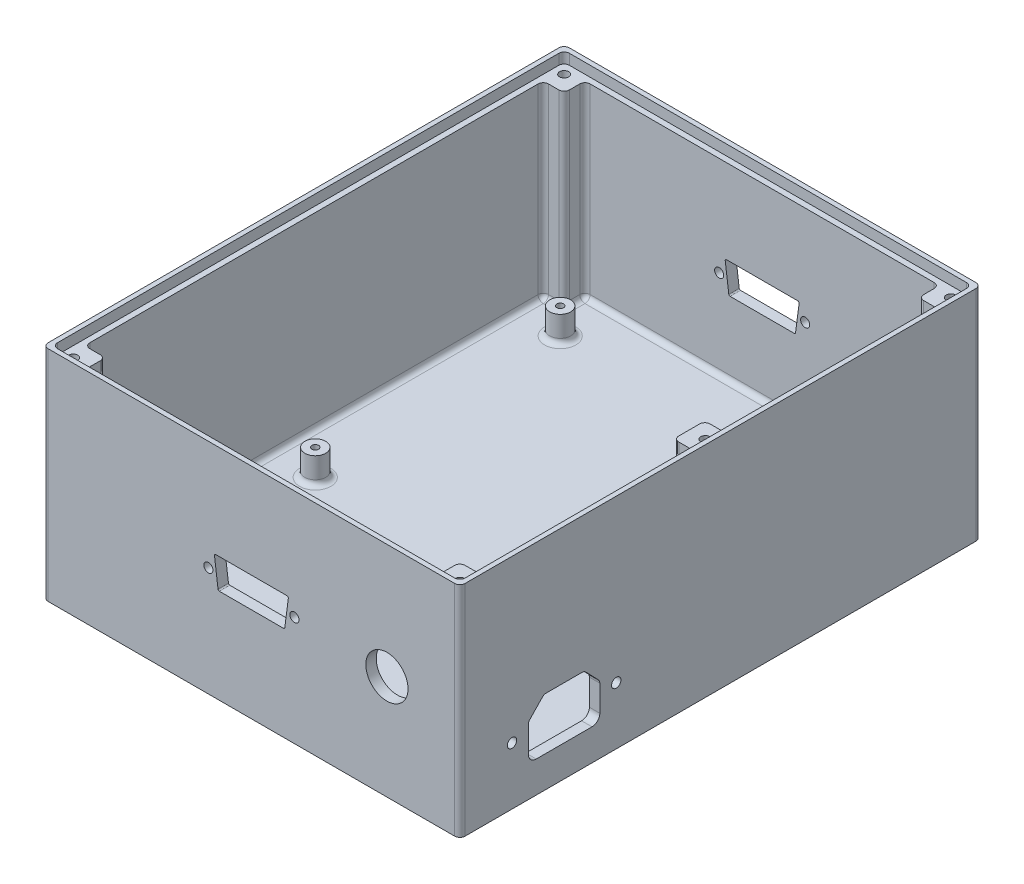
SolidWorks part; units mm, degrees
ref_plane "Front Plane" through (0, 0, 0) normal (0, 0, 1) x (1, 0, 0)
ref_plane "Top Plane" through (0, 0, 0) normal (0, 1, 0) x (1, 0, 0)
ref_plane "Right Plane" through (0, 0, 0) normal (1, 0, 0) x (0, 0, -1)
sketch "Esboço1" plane through (0, 0, 0) normal (1, 0, 0) x (0, 0, -1)
  line L0 (-100, 0) -> (100, 0)
  line L1 (100, 0) -> (100, 84)
  line L2 (100, 84) -> (-100, 84)
  line L3 (-100, 84) -> (-100, 0)
  point P4 (0, 0)
  dimension "D1" = 84
  dimension "D2" = 200
extrude "Ressalto-extrusão1" add sketch "Esboço1" along normal mid plane 160
sketch "Esboço4" plane through (0, 84, 0) normal (0, 1, 0) x (1, 0, 0)
  line L0 (0, 100) -> (0, -100) construction
  line L1 (80, 100) -> (-80, 100) construction
  line L2 (80, -100) -> (-80, -100) construction
  line L3 (-80, 0) -> (80, 0) construction
  line L4 (-80, 100) -> (-80, -100) construction
  line L5 (80, 100) -> (80, -100) construction
  line L6 (-68, -96) -> (68, -96)
  line L7 (68, -96) -> (68, -88)
  line L8 (68, -88) -> (76, -88)
  line L9 (76, -88) -> (76, -6)
  line L10 (-68, -96) -> (-68, -88)
  line L11 (-68, -88) -> (-76, -88)
  line L12 (76, -6) -> (68, -6)
  line L13 (68, -6) -> (68, 6)
  line L14 (68, 6) -> (76, 6)
  line L15 (76, 6) -> (76, 88)
  line L16 (76, 88) -> (68, 88)
  line L17 (68, 88) -> (68, 96)
  line L18 (68, 96) -> (-68, 96)
  line L19 (-68, 96) -> (-68, 88)
  line L20 (-68, 88) -> (-76, 88)
  line L21 (-76, 88) -> (-76, -88)
  circle A0 centre (-74.2, -94.2) radius 1.75
  circle A1 centre (-74.2, 94.2) radius 1.75
  circle A2 centre (74.2, -94.2) radius 1.75
  circle A3 centre (74.2, 94.2) radius 1.75
  circle A4 centre (74.2, 0) radius 1.75
  dimension "D8" = 3.5
  dimension "D2" = 4
  dimension "D3" = 12
  dimension "D4" = 6
  dimension "D5" = 12
  dimension "D6" = 6
  dimension "D7" = 4
  dimension "D9" = 5.8
  dimension "D10" = 5.8
  dimension "D11" = 5.8
  dimension "D12" = 4
extrude "Corte-extrusão1" cut sketch "Esboço4" against normal blind 76
fillet "Filete1" radius 2 10 edges at (-68, 46, 88) (-68, 46, -88) (68, 46, -88) (68, 46, 6) (68, 46, -6) (68, 46, 88) (80, 42, 100) (-80, 42, 100) (-80, 42, -100) (80, 42, -100)
sketch "Esboço7" plane through (0, 0, 0) normal (0, 0, 1) x (1, 0, 0)
  line L0 (0, 84) -> (0, 0) construction
  line L1 (78, 84) -> (-78, 84) construction
  line L2 (-80, 42) -> (80, 42) construction
  line L3 (-80, 0) -> (-80, 84) construction
  line L4 (80, 84) -> (80, 0) construction
  line L13 (-12.75, 36.25) -> (12.75, 36.25)
  line L16 (-14.25, 47.75) -> (14.25, 47.75)
  line L17 (-14.25, 47.75) -> (-12.75, 36.25)
  line L18 (14.25, 47.75) -> (12.75, 36.25)
  circle A0 centre (-16.5, 42) radius 1.75
  circle A2 centre (16.5, 42) radius 1.75
  point P21 (0, 42)
  point P22 (0, 36.25)
  point P23 (0, 47.75)
  point P24 (0, 42)
  dimension "D1" = 3.5
  dimension "D2" = 14.25
  dimension "D3" = 12.75
  dimension "D4" = 5.75
  dimension "D5" = 16.5
  dimension "D6" = 11.5
  dimension "D7" = 0
extrude "Corte-extrusão2" cut sketch "Esboço7" against normal mid plane 200
fillet "Filete3" radius 0.5 8 edges at (14.25, 47.75, -98) (-14.25, 47.75, -98) (-12.75, 36.25, -98) (12.75, 36.25, -98) (14.25, 47.75, 98) (12.75, 36.25, 98) (-12.75, 36.25, 98) (-14.25, 47.75, 98)
sketch "Esboço8" plane through (0, 0, 100) normal (0, 0, -1) x (-1, 0, 0)
  line L0 (-80, 0) -> (-80, 84) construction
  line L2 (-78, 0) -> (78, 0) construction
  circle A0 centre (-52, 40) radius 8.1
  dimension "D1" = 16.2
  dimension "D2" = 28
  dimension "D3" = 40
extrude "Corte-extrusão3" cut sketch "Esboço8" against normal up to surface (196 mm away)
sketch "Esboço9" plane through (0, 8, 0) normal (0, 1, 0) x (1, 0, 0)
  line L8 (-80, 98) -> (-80, -98) construction
  line L9 (78, 100) -> (-78, 100) construction
  line L10 (-68, -96) -> (68, -96) construction
  line L11 (0, 100) -> (0, -100) construction
  line L12 (-80, 31.5) -> (80, 31.5) construction
  line L13 (80, 98) -> (80, -98) construction
  line L14 (78, -100) -> (-78, -100) construction
  line L16 (-76, 88) -> (-76, -88) construction
  line L19 (-68, -96) -> (68, -96) construction
  circle A0 centre (-60, 78.5) radius 4
  circle A1 centre (-60, 78.5) radius 1.3
  circle A2 centre (60, 78.5) radius 1.3
  circle A3 centre (60, 78.5) radius 4
  circle A4 centre (60, -15.5) radius 4
  circle A5 centre (60, -15.5) radius 1.3
  circle A6 centre (-60, -15.5) radius 1.3
  circle A7 centre (-60, -15.5) radius 4
  circle A8 centre (-46, -86) radius 4
  circle A9 centre (-46, -86) radius 1.75
  circle A10 centre (0, -86) radius 4
  circle A11 centre (0, -86) radius 1.75
  dimension "D5" = 2.6
  dimension "D6" = 8
  dimension "D4" = 10
  dimension "D10" = 3.5
  dimension "D11" = 8
  dimension "D12" = 21.5
  dimension "D2" = 16
  dimension "D3" = 68.5
  dimension "D7" = 10
  dimension "D8" = 46
  dimension "D9" = 30
extrude "Ressalto-extrusão2" add sketch "Esboço9" along normal blind 10
sketch "Esboço11" plane through (80, 0, 0) normal (1, 0, 0) x (0, 0, -1)
  line L2 (-73.7, 15) -> (-73.7, 25.7908)
  line L3 (-70.7, 12) -> (-49.3, 12)
  line L4 (-73.7, 25.7908) -> (-67.7497, 32)
  line L5 (-67.7497, 32) -> (-52.2503, 32)
  line L6 (-60, 12) -> (-60, 32) construction
  line L7 (-46.3, 25.7908) -> (-52.2503, 32)
  line L8 (-46.3, 15) -> (-46.3, 25.7908)
  line L9 (-100, 0) -> (-100, 84) construction
  line L10 (98, 84) -> (-98, 84) construction
  line L13 (-60, 22) -> (-84.4967, 22) construction
  line L14 (-84.4967, 22) -> (-36.6459, 22) construction
  arc A1 (-73.7, 15) -> (-70.7, 12) centre (-70.7, 15) ccw
  arc A2 (-46.3, 15) -> (-49.3, 12) centre (-49.3, 15) cw
  circle A4 centre (-80, 22) radius 1.8
  circle A5 centre (-40, 22) radius 1.8
  point P21 (-60, 22)
  dimension "D1" = 133.78
  dimension "D4" = 3
  dimension "D8" = 3.6
  dimension "D2" = 8.6
  dimension "D3" = 10
  dimension "D5" = 13.7
  dimension "D6" = 40
  dimension "D7" = 52
  dimension "D9" = 20
extrude "Corte-extrusão4" cut sketch "Esboço11" against normal up to surface (4 mm away) up to face at (76, 46, 47)
fillet "Filete4" radius 2 10 edges at (76, 46, -6) (76, 46, 6) (68, 46, -96) (76, 46, -88) (-76, 46, -88) (-68, 46, -96) (-76, 46, 88) (-68, 46, 96) (68, 46, 96) (76, 46, 88)
fillet "Filete5" radius 2 38 edges at (-68.5858, 8, 88.5858) (-75.4142, 8, 87.4142) (-76, 8, 0) (-75.4142, 8, -87.4142) (-68.5858, 8, -88.5858) (-67.4142, 8, -95.4142) (0, 8, -96) (67.4142, 8, -95.4142) (68.5858, 8, -88.5858) (75.4142, 8, -87.4142) (76, 8, -47) (75.4142, 8, -6.5858) (68.5858, 8, -5.4142) (68, 8, 0) (68.5858, 8, 5.4142) (75.4142, 8, 6.5858) (76, 8, 47) (75.4142, 8, 87.4142) (68.5858, 8, 88.5858) (67.4142, 8, 95.4142) (0, 8, 96) (-60, 8, -74.5) (60, 8, -82.5) (60, 8, 19.5) (-60, 8, 11.5) (0, 8, 90) (-46, 8, 90) (-67.4142, 8, 95.4142) (-68, 8, 92) (-72, 8, 88) (-72, 8, -88) (-68, 8, -92) (68, 8, -92) (72, 8, -88) (72, 8, -6) (72, 8, 6) (72, 8, 88) (68, 8, 92)
fillet "Filete7" radius 2 4 edges at (78, 25.7908, 73.7) (78, 32, 67.7497) (78, 32, 52.2503) (78, 25.7908, 46.3)
sketch "Esboço17" plane through (0, 84, 0) normal (0, 1, 0) x (1, 0, 0)
  line L1 (78, 100) -> (-78, 100) construction
  line L2 (-78.2, 98.2) -> (-78.2, -98.2)
  line L3 (0, 100) -> (0, -100) construction
  line L5 (78, -100) -> (-78, -100) construction
  line L6 (78.2, 98.2) -> (-78.2, 98.2)
  line L7 (-80, 0) -> (80, 0) construction
  line L8 (-80, 98) -> (-80, -98) construction
  line L9 (80, 98) -> (80, -98) construction
  line L10 (78.2, 98.2) -> (78.2, -98.2)
  line L11 (78.2, -98.2) -> (-78.2, -98.2)
  point P19 (0, 98.2)
  point P20 (78.2, 0)
  point P21 (-78.2, 0)
  dimension "D1" = 1.8
  dimension "D2" = 1.8
extrude "Corte-extrusão8" cut sketch "Esboço17" against normal blind 4
fillet "Filete10" radius 2 4 edges at (78.2, 82, -98.2) (78.2, 82, 98.2) (-78.2, 82, 98.2) (-78.2, 82, -98.2)
